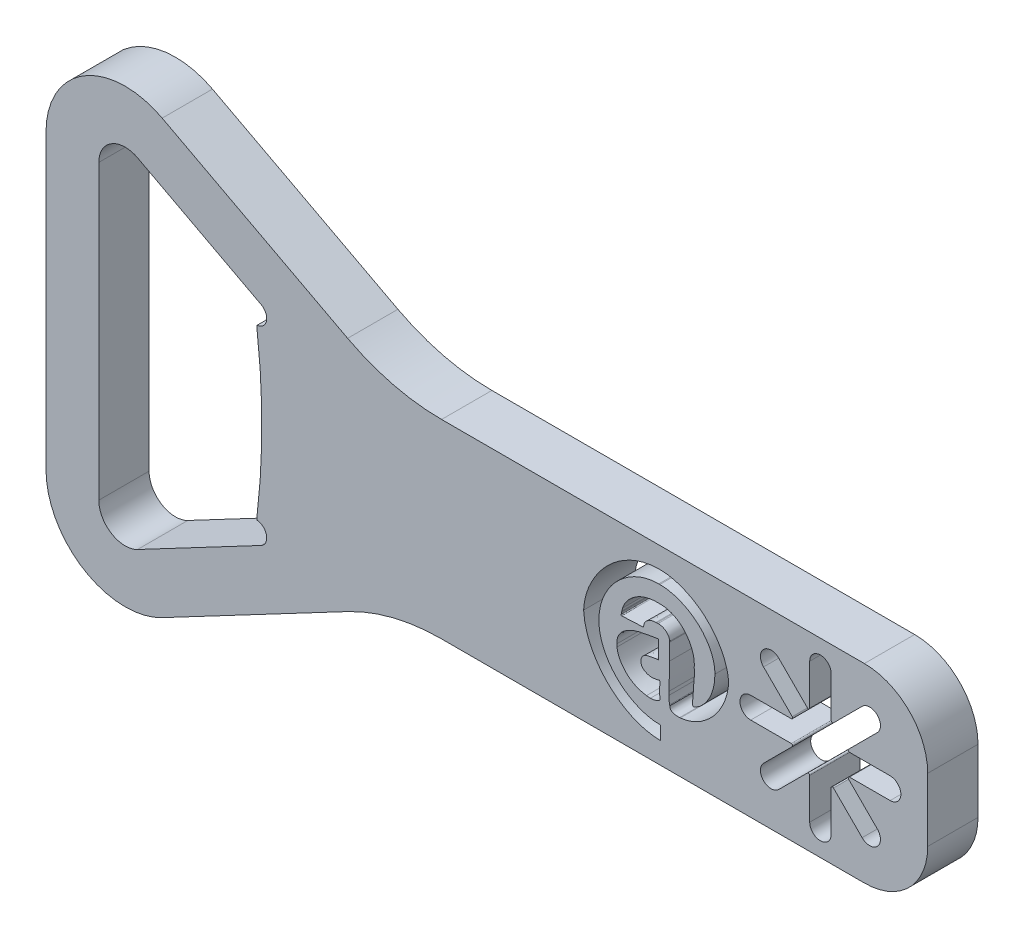
SolidWorks part; units mm, degrees
ref_plane "Front Plane" through (0, 0, 0) normal (0, 0, 1) x (1, 0, 0)
ref_plane "Top Plane" through (0, 0, 0) normal (0, 1, 0) x (1, 0, 0)
ref_plane "Right Plane" through (0, 0, 0) normal (1, 0, 0) x (0, 0, -1)
sketch "Model" plane through (0, 0, 0) normal (0, 0, 1) x (1, 0, 0)
  line L0 (93.451, 245.0307) -> (75.8892, 254.3082)
  line L1 (64.8859, 247.6767) -> (64.8859, 219.9729)
  line L2 (75.8892, 213.3414) -> (93.451, 222.6188)
  line L3 (102.3493, 224.8248) -> (142.3859, 224.8248)
  line L4 (73.5537, 217.7624) -> (85.2574, 223.9452)
  line L5 (69.8859, 247.6767) -> (69.8859, 219.9729)
  line L6 (85.2574, 243.7044) -> (73.5537, 249.8872)
  line L7 (84.8859, 225.8248) -> (84.8859, 226.3248)
  line L8 (84.8859, 241.3248) -> (84.8859, 241.8248)
  line L9 (142.3859, 242.8248) -> (102.3493, 242.8248)
  line L10 (148.3859, 230.8248) -> (148.3859, 236.8248)
  arc A0 (93.451, 245.0307) -> (102.3493, 242.8248) centre (102.3493, 261.8748) ccw
  arc A1 (75.8892, 254.3082) -> (64.8859, 247.6767) centre (72.3859, 247.6767) ccw
  arc A2 (64.8859, 219.9729) -> (75.8892, 213.3414) centre (72.3859, 219.9729) ccw
  arc A3 (102.3493, 224.8248) -> (93.451, 222.6188) centre (102.3493, 205.7748) ccw
  arc A4 (69.8859, 219.9729) -> (73.5537, 217.7624) centre (72.3859, 219.9729) ccw
  arc A5 (73.5537, 249.8872) -> (69.8859, 247.6767) centre (72.3859, 247.6767) ccw
  arc A6 (85.2574, 223.9452) -> (85.7424, 225.1352) centre (84.7903, 224.8294) ccw
  arc A7 (85.7424, 242.5144) -> (85.2574, 243.7044) centre (84.7903, 242.8202) ccw
  arc A9 (85.7424, 225.1352) -> (84.8859, 225.8248) centre (84.7903, 224.8294) ccw
  arc A10 (84.8859, 226.3248) -> (84.8859, 241.3248) centre (21.8304, 233.8248) ccw
  arc A11 (84.8859, 241.8248) -> (85.7424, 242.5144) centre (84.7903, 242.8202) ccw
  arc A12 (148.3859, 236.8248) -> (142.3859, 242.8248) centre (142.3859, 236.8248) ccw
  arc A13 (142.3859, 224.8248) -> (148.3859, 230.8248) centre (142.3859, 230.8248) ccw
extrude "Boss-Extrude1" add sketch "Model" along normal blind 4.7625
sketch "Sketch2" plane through (0, 0, 4.7625) normal (0, 0, 1) x (1, 0, 0)
  line L8 (136.9559, 226.9668) -> (136.9559, 230.7587)
  line L9 (139.4959, 226.9668) -> (139.4959, 230.7587)
  line L11 (132.4785, 229.8735) -> (135.1599, 232.5548)
  line L12 (134.2746, 228.0774) -> (136.9559, 230.7587)
  line L14 (131.3679, 235.0948) -> (135.1599, 235.0948)
  line L15 (131.3679, 232.5548) -> (135.1599, 232.5548)
  line L17 (134.2746, 239.5721) -> (136.9559, 236.8908)
  line L18 (132.4785, 237.7761) -> (135.1599, 235.0948)
  line L19 (136.9559, 236.8908) -> (136.9559, 240.6828)
  line L21 (139.4959, 236.8908) -> (142.1772, 239.5721)
  line L22 (139.4959, 236.8908) -> (139.4959, 240.6828)
  line L23 (141.292, 235.0948) -> (145.0839, 235.0948)
  line L24 (141.292, 235.0948) -> (143.9733, 237.7761)
  line L25 (141.292, 232.5548) -> (143.9733, 229.8735)
  line L26 (141.292, 232.5548) -> (145.0839, 232.5548)
  line L28 (139.4959, 230.7587) -> (142.1772, 228.0774)
  arc A0 (136.9559, 226.9668) -> (139.4959, 226.9668) centre (138.2259, 226.9668) ccw
  arc A1 (139.4959, 240.6828) -> (136.9559, 240.6828) centre (138.2259, 240.6828) ccw
  arc A2 (132.4785, 229.8735) -> (134.2746, 228.0774) centre (133.3766, 228.9754) ccw
  arc A3 (143.9733, 237.7761) -> (142.1772, 239.5721) centre (143.0752, 238.6741) ccw
  arc A4 (131.3679, 235.0948) -> (131.3679, 232.5548) centre (131.3679, 233.8248) ccw
  arc A5 (145.0839, 232.5548) -> (145.0839, 235.0948) centre (145.0839, 233.8248) ccw
  arc A6 (134.2746, 239.5721) -> (132.4785, 237.7761) centre (133.3766, 238.6741) ccw
  arc A7 (142.1772, 228.0774) -> (143.9733, 229.8735) centre (143.0752, 228.9754) ccw
  dimension "D4" = 2.54
  dimension "D5" = 2.54
  dimension "D6" = 2.54
  dimension "D7" = 2.54
extrude "Cut-Extrude1" [suppressed] cut sketch "Sketch2" against normal through all
fillet "Fillet1" [suppressed] radius 0.127
sketch "Sketch3" plane through (0, 0, 4.7625) normal (0, 0, 1) x (1, 0, 0)
  line L0 (144.5037, 232.5943) -> (85.3304, 232.5943) construction
  text T0 "@secret_buttholes" font "Stencilia-Bold" height in points 12
  point P2 (144.5037, 233.8248)
  point P3 (0, 0)
  point P4 (85.3304, 233.8248)
  point P9 (148.3859, 233.8248)
extrude "Cut-Extrude2" [suppressed] cut sketch "Sketch3" against normal through all
sketch "Sketch4" plane through (0, 0, 4.7625) normal (0, 0, 1) x (1, 0, 0)
  line L8 (137.2099, 227.2231) -> (137.2099, 231.3719)
  line L9 (139.2419, 227.2231) -> (139.2419, 231.3719)
  line L11 (132.8394, 229.8751) -> (135.7731, 232.8088)
  line L12 (134.2762, 228.4383) -> (137.2099, 231.3719)
  line L14 (131.6242, 234.8408) -> (135.7731, 234.8408)
  line L15 (131.6242, 232.8088) -> (135.7731, 232.8088)
  line L17 (134.2762, 239.2113) -> (137.2099, 236.2776)
  line L18 (132.8394, 237.7745) -> (135.7731, 234.8408)
  line L19 (137.2099, 236.2776) -> (137.2099, 240.4265)
  line L20 (139.2419, 236.2776) -> (142.1756, 239.2113)
  line L30 (140.6788, 232.8088) -> (144.8276, 232.8088)
  line L31 (139.2419, 231.3719) -> (142.1756, 228.4383)
  line L39 (139.2419, 236.2776) -> (139.2419, 240.4265)
  line L40 (140.6788, 234.8408) -> (144.8276, 234.8408)
  line L41 (140.6788, 234.8408) -> (143.6124, 237.7745)
  line L42 (140.6788, 232.8088) -> (143.6124, 229.8751)
  arc A0 (137.2099, 227.2231) -> (139.2419, 227.2231) centre (138.2259, 227.2231) ccw
  arc A1 (139.2419, 240.4265) -> (137.2099, 240.4265) centre (138.2259, 240.4265) ccw
  arc A2 (132.8394, 229.8751) -> (134.2762, 228.4383) centre (133.5578, 229.1567) ccw
  arc A3 (143.6124, 237.7745) -> (142.1756, 239.2113) centre (142.894, 238.4929) ccw
  arc A4 (131.6242, 234.8408) -> (131.6242, 232.8088) centre (131.6242, 233.8248) ccw
  arc A5 (144.8276, 232.8088) -> (144.8276, 234.8408) centre (144.8276, 233.8248) ccw
  arc A6 (134.2762, 239.2113) -> (132.8394, 237.7745) centre (133.5578, 238.4929) ccw
  arc A7 (142.1756, 228.4383) -> (143.6124, 229.8751) centre (142.894, 229.1567) ccw
  dimension "D2" = 2.032
  dimension "D3" = 2.032
  dimension "D4" = 2.032
  dimension "D5" = 2.032
extrude "Cut-Extrude3" cut sketch "Sketch4" against normal through all
sketch "Sketch5" plane through (0, 0, 4.7625) normal (0, 0, 1) x (1, 0, 0)
  line L0 (113.9665, 228.8809) -> (126.1205, 228.8809) construction
  text T0 "@" font "Stencilia-Bold" height in points 40
  point P3 (120.3656, 229.303)
  point P4 (117.5703, 229.9607)
  point P5 (115.7616, 229.5497)
  point P6 (113.3774, 229.5497)
  point P7 (0, 0)
  point P8 (0, 0)
  point P9 (112.2264, 229.303)
  point P10 (113.9665, 228.8809)
extrude "Cut-Extrude4" cut sketch "Sketch5" against normal through all
fillet "Fillet2" radius 0.127 9 edges at (139.2419, 236.2776, 2.3813) (140.6788, 234.8408, 2.3813) (139.2419, 231.3719, 2.3813) (140.6788, 232.8088, 2.3813) (137.2099, 231.3719, 2.3813) (135.7731, 232.8088, 2.3813) (135.7731, 234.8408, 2.3813) (137.2099, 236.2776, 2.3813) (126.0959, 231.1377, 2.3813)
